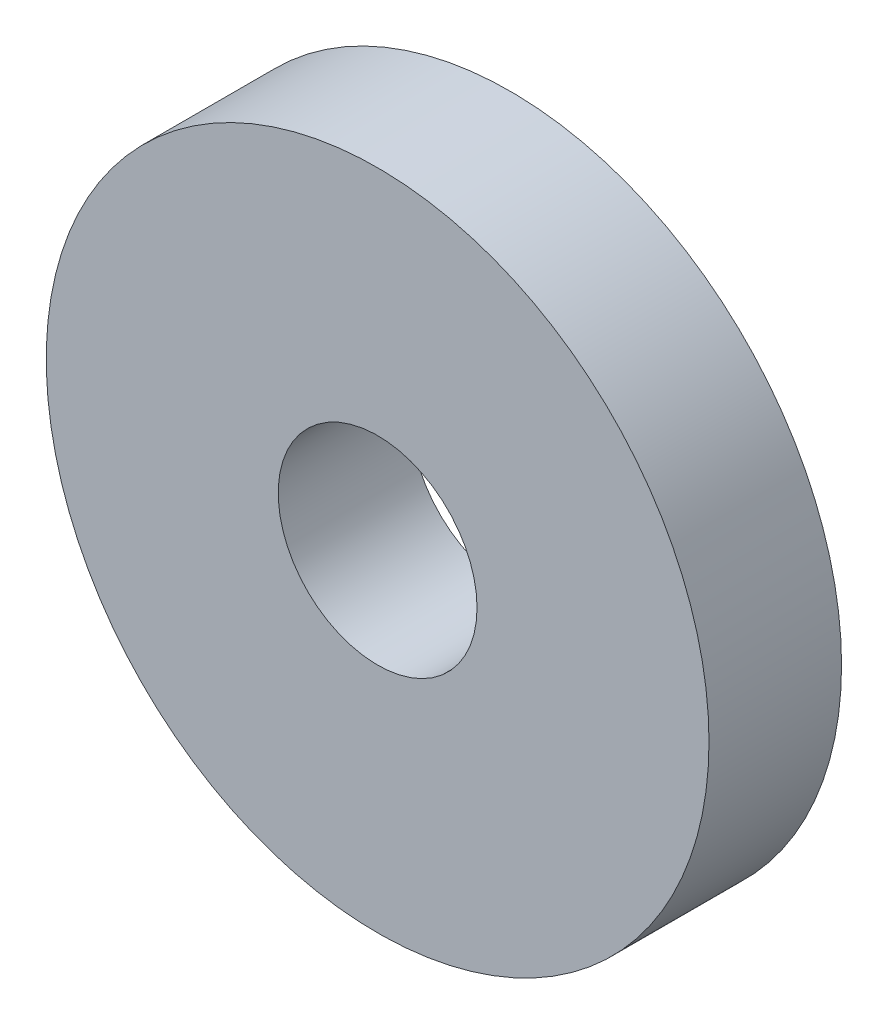
SolidWorks part; units mm, degrees
ref_plane "前视基准面" through (0, 0, 0) normal (0, 0, 1) x (1, 0, 0)
ref_plane "上视基准面" through (0, 0, 0) normal (0, 1, 0) x (1, 0, 0)
ref_plane "右视基准面" through (0, 0, 0) normal (1, 0, 0) x (0, 0, -1)
sketch "草图1" plane through (0, 0, 0) normal (0, 0, 1) x (1, 0, 0)
  circle A0 centre (0, 0) radius 3
  circle A1 centre (0, 0) radius 10
extrude "凸台-拉伸1" add sketch "草图1" along normal blind 4
